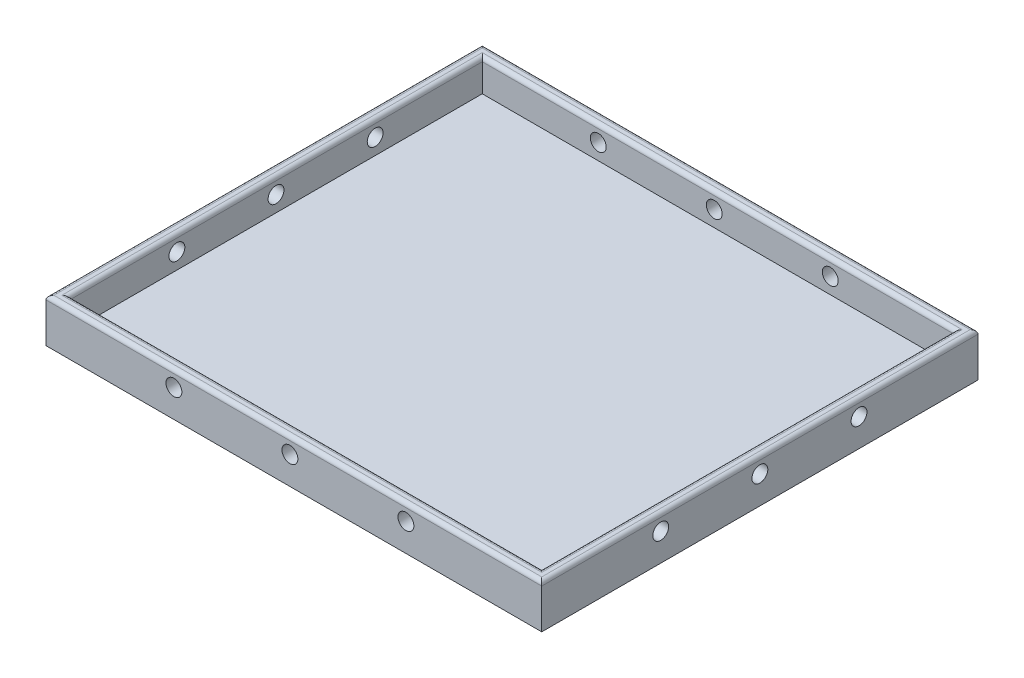
SolidWorks part; units mm, degrees
ref_plane "Front Plane" through (0, 0, 0) normal (0, 0, 1) x (1, 0, 0)
ref_plane "Top Plane" through (0, 0, 0) normal (0, 1, 0) x (1, 0, 0)
ref_plane "Right Plane" through (0, 0, 0) normal (1, 0, 0) x (0, 0, -1)
sketch "Sketch1" plane through (0, 0, 0) normal (0, 1, 0) x (1, 0, 0)
  line L1 (-201.6099, 77.8947) -> (-76.6099, 77.8947)
  line L2 (-201.6099, 77.8947) -> (-201.6099, -32.1053)
  line L3 (-201.6099, -32.1053) -> (-76.6099, -32.1053)
  line L4 (-76.6099, 77.8947) -> (-76.6099, -32.1053)
  dimension "D1" = 125
  dimension "D2" = 110
extrude "Boss-Extrude1" add sketch "Sketch1" along normal blind 11
sketch "Sketch4" plane through (0, 11, 0) normal (0, 1, 0) x (1, 0, 0)
  line L0 (-201.6099, 77.8947) -> (-201.6099, -32.1053) construction
  line L1 (-198.6099, 74.8947) -> (-79.6099, 74.8947)
  line L2 (-198.6099, 74.8947) -> (-198.6099, -29.1053)
  line L3 (-198.6099, -29.1053) -> (-79.6099, -29.1053)
  line L4 (-79.6099, 74.8947) -> (-79.6099, -29.1053)
  line L5 (-76.6099, 77.8947) -> (-201.6099, 77.8947) construction
  line L6 (-76.6099, -32.1053) -> (-76.6099, 77.8947) construction
  line L7 (-201.6099, -32.1053) -> (-76.6099, -32.1053) construction
  dimension "D1" = 3
  dimension "D2" = 3
  dimension "D3" = 3
  dimension "D4" = 3
extrude "Cut-Extrude1" cut sketch "Sketch4" against normal blind 8
sketch "Sketch5" plane through (0, 0, -74.8947) normal (0, 0, 1) x (1, 0, 0)
  line L0 (-198.6099, 3) -> (-198.6099, 11) construction
  line L1 (-79.6099, 3) -> (-198.6099, 3) construction
  circle A0 centre (-169.3599, 7) radius 2
  circle A1 centre (-140.1099, 7) radius 2
  circle A2 centre (-110.8599, 7) radius 2
  dimension "D1" = 29.25
  dimension "D2" = 29.25
  dimension "D3" = 29.25
  dimension "D4" = 4
  dimension "D5" = 4
  dimension "D6" = 4
sketch "Sketch6" plane through (-198.6099, 0, 0) normal (1, 0, 0) x (0, 0, -1)
  line L0 (-29.1053, 3) -> (-29.1053, 11) construction
  line L1 (74.8947, 3) -> (74.8947, 11) construction
  line L2 (74.8947, 3) -> (-29.1053, 3) construction
  circle A0 centre (-2.1053, 7) radius 2
  circle A1 centre (22.8947, 7) radius 2
  circle A2 centre (47.8947, 7) radius 2
  dimension "D1" = 27
  dimension "D2" = 25
  dimension "D3" = 25
  dimension "D4" = 27
  dimension "D5" = 4
extrude "Cut-Extrude6" cut sketch "Sketch6" against normal through all both and the other way through all
extrude "Cut-Extrude5" cut sketch "Sketch5" against normal through all both and the other way through all
fillet "Fillet2" radius 1 8 edges at (-139.1099, 11, 29.1053) (-139.1099, 11, 32.1053) (-76.6099, 11, -22.8947) (-79.6099, 11, -22.8947) (-198.6099, 11, -22.8947) (-139.1099, 11, -74.8947) (-201.6099, 11, -22.8947) (-139.1099, 11, -77.8947)
